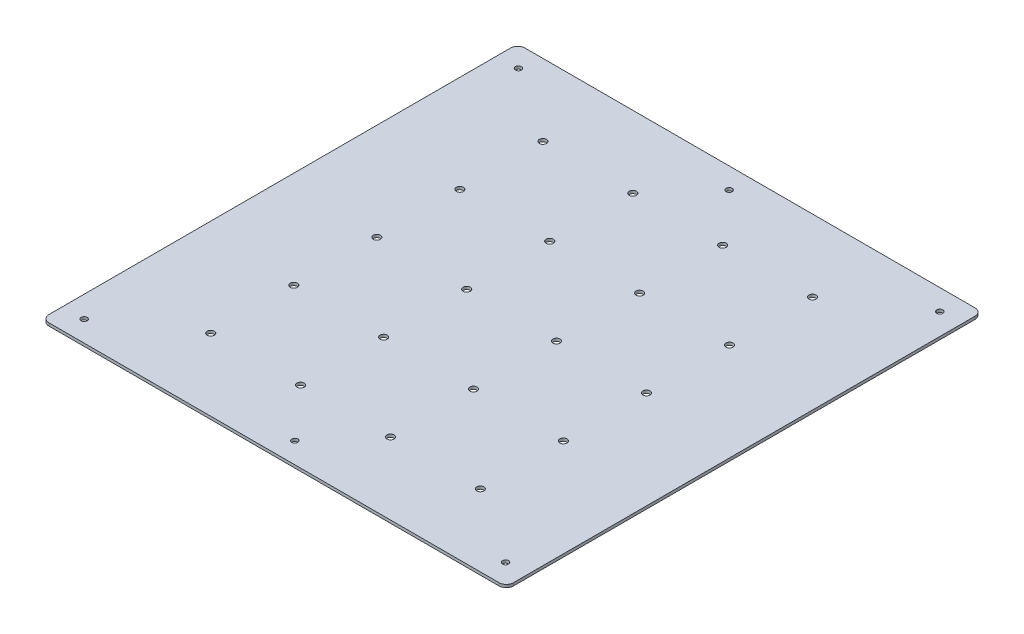
SolidWorks part; units mm, degrees
ref_plane "Front Plane" through (0, 0, 0) normal (0, 0, 1) x (1, 0, 0)
ref_plane "Top Plane" through (0, 0, 0) normal (0, 1, 0) x (1, 0, 0)
ref_plane "Right Plane" through (0, 0, 0) normal (1, 0, 0) x (0, 0, -1)
sketch "Sketch1" plane through (0, 0, 0) normal (0, 1, 0) x (1, 0, 0)
  line L0 (-161.5, 160.5) -> (-161.5, -160.5)
  line L1 (-156.5, -165.5) -> (156.5, -165.5)
  line L2 (161.5, -160.5) -> (161.5, 160.5)
  line L3 (156.5, 165.5) -> (-156.5, 165.5)
  arc A0 (-156.5, 165.5) -> (-161.5, 160.5) centre (-156.5, 160.5) ccw
  arc A1 (-161.5, -160.5) -> (-156.5, -165.5) centre (-156.5, -160.5) ccw
  arc A2 (156.5, -165.5) -> (161.5, -160.5) centre (156.5, -160.5) ccw
  arc A3 (161.5, 160.5) -> (156.5, 165.5) centre (156.5, 160.5) ccw
  circle A4 centre (0, 151) radius 2.1
  circle A5 centre (146.5, 151) radius 2.1
  circle A6 centre (-146.5, 151) radius 2.1
  circle A7 centre (0, -151) radius 2.1
  circle A8 centre (146.5, -151) radius 2.1
  circle A9 centre (-146.5, -151) radius 2.1
  circle A10 centre (-94, 115.5) radius 2.5
  circle A11 centre (-31.5, 115.5) radius 2.5
  circle A12 centre (31, 115.5) radius 2.5
  circle A13 centre (93.5, 115.5) radius 2.5
  circle A14 centre (-94, 57.75) radius 2.5
  circle A15 centre (-31.5, 57.75) radius 2.5
  circle A16 centre (31, 57.75) radius 2.5
  circle A17 centre (93.5, 57.75) radius 2.5
  circle A18 centre (-94, 0) radius 2.5
  circle A19 centre (-31.5, 0) radius 2.5
  circle A20 centre (31, 0) radius 2.5
  circle A21 centre (93.5, 0) radius 2.5
  circle A22 centre (-94, -57.75) radius 2.5
  circle A23 centre (-31.5, -57.75) radius 2.5
  circle A24 centre (31, -57.75) radius 2.5
  circle A25 centre (93.5, -57.75) radius 2.5
  circle A26 centre (-94, -115.5) radius 2.5
  circle A27 centre (-31.5, -115.5) radius 2.5
  circle A28 centre (31, -115.5) radius 2.5
  circle A29 centre (93.5, -115.5) radius 2.5
extrude "Boss-Extrude1" add sketch "Sketch1" along normal mid plane 2
